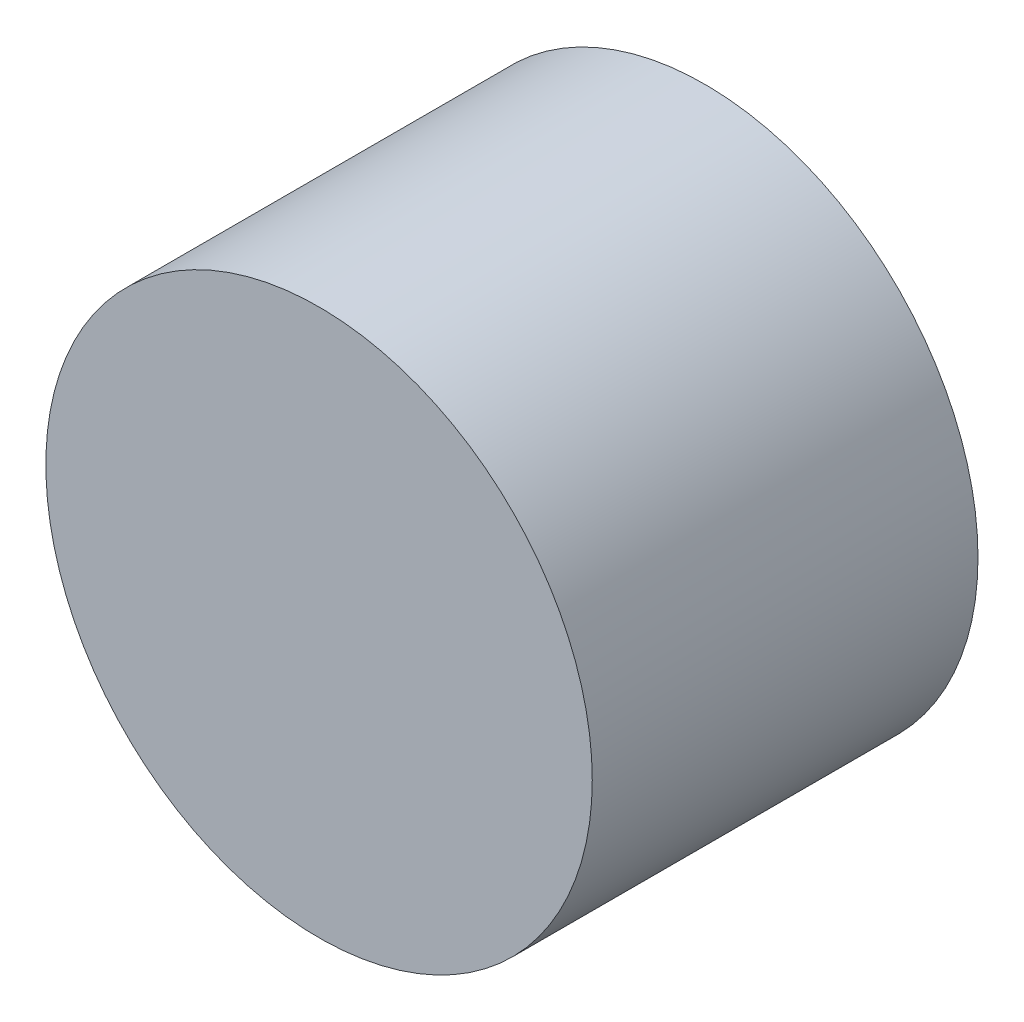
SolidWorks part; units mm, degrees
ref_plane "Front" through (0, 0, 0) normal (0, 0, 1) x (1, 0, 0)
ref_plane "Top" through (0, 0, 0) normal (0, 1, 0) x (1, 0, 0)
ref_plane "Right" through (0, 0, 0) normal (1, 0, 0) x (0, 0, -1)
sketch "Sketch1" plane through (0, 0, 0) normal (0, 0, 1) x (1, 0, 0)
  circle A0 centre (0, 0) radius 8.5
  dimension "D1" = 17
extrude "Boss-Extrude1" add sketch "Sketch1" along normal blind 12
